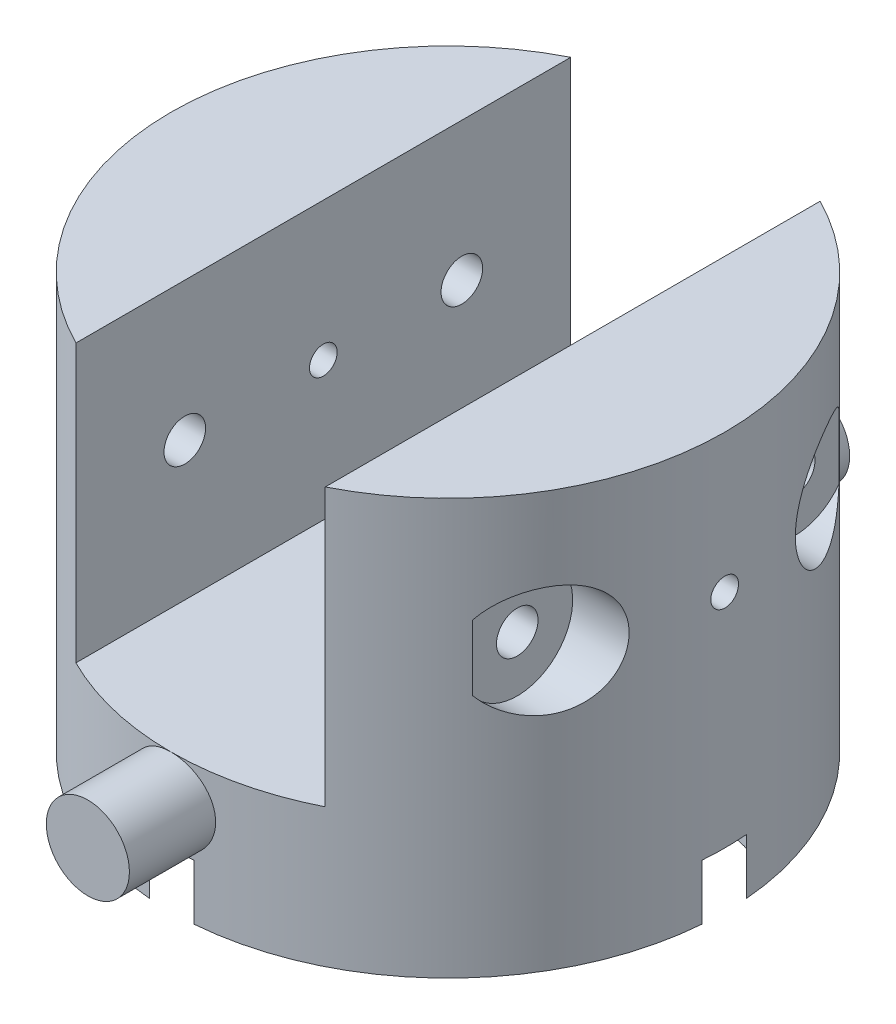
SolidWorks part; units mm, degrees
ref_plane "Front Plane" through (0, 0, 0) normal (0, 0, 1) x (1, 0, 0)
ref_plane "Top Plane" through (0, 0, 0) normal (0, 1, 0) x (1, 0, 0)
ref_plane "Right Plane" through (0, 0, 0) normal (1, 0, 0) x (0, 0, -1)
sketch "Sketch1" plane through (0, 0, 0) normal (0, 1, 0) x (1, 0, 0)
  circle A0 centre (0, 0) radius 10
  circle A1 centre (0, 0) radius 2.5
  dimension "D1" = 20
  dimension "D2" = 5
extrude "Boss-Extrude1" add sketch "Sketch1" along normal blind 5
ref_plane "Plane1" through (0, 0, 10) normal (0, 0, 1) x (1, 0, 0)
sketch "Sketch5" plane through (0, 5, 0) normal (0, 1, 0) x (1, 0, 0)
  line L1 (0, 0) -> (0, 3.5) construction
  line L5 (4.5, 8.9303) -> (4.5, -8.9303)
  line L6 (-4.5, 8.9303) -> (-4.5, -8.9303)
  arc A2 (-4.5, 8.9303) -> (-4.5, -8.9303) centre (0, 0) ccw
  arc A4 (4.5, -8.9303) -> (4.5, 8.9303) centre (0, 0) ccw
  dimension "D1" = 20
  dimension "D2" = 4.5
extrude "Boss-Extrude4" add sketch "Sketch5" along normal blind 10
ref_plane "Plane2" through (-10, 0, 0) normal (-1, 0, 0) x (0, 0, 1)
sketch "Sketch6" plane through (-10, 0, 0) normal (-1, 0, 0) x (0, 0, 1)
  line L0 (8.9303, 15) -> (-8.9303, 15) construction
  line L2 (0, 15) -> (0, 5) construction
  line L3 (10, 5) -> (-10, 5) construction
  line L4 (-8.9303, 5) -> (-10, 5) construction
  circle A0 centre (-5, 10) radius 0.75
  circle A1 centre (5, 10) radius 0.75
  dimension "D1" = 1.5
  dimension "D2" = 5
  dimension "D3" = 5
extrude "Cut-Extrude3" cut sketch "Sketch6" against normal through all contours A0 | A1
sketch "Sketch7" plane through (-10, 0, 0) normal (-1, 0, 0) x (0, 0, 1)
  line L0 (0, 5) -> (0, 15) construction
  line L1 (10, 5) -> (-10, 5) construction
  line L2 (8.9303, 15) -> (-8.9303, 15) construction
  circle A0 centre (-5, 10) radius 2
  circle A1 centre (5, 10) radius 2
  dimension "D1" = 4
extrude "Cut-Extrude4" cut sketch "Sketch7" against normal blind 2.5
ref_plane "Plane3" through (10, 0, 0) normal (1, 0, 0) x (0, 0, -1)
sketch "Sketch8" plane through (10, 0, 0) normal (1, 0, 0) x (0, 0, -1)
  line L0 (0, 5) -> (0, 15) construction
  line L7 (10, 5) -> (-10, 5) construction
  line L8 (8.9303, 15) -> (-8.9303, 15) construction
  circle A0 centre (-5, 10) radius 2
  circle A1 centre (5, 10) radius 2
  dimension "D1" = 4
extrude "Cut-Extrude5" cut sketch "Sketch8" against normal blind 2.5
ref_plane "Plane4" through (0, 0, 10) normal (0, 0, 1) x (1, 0, 0)
sketch "Sketch10" plane through (0, 0, 10) normal (0, 0, 1) x (1, 0, 0)
  line L0 (0, 0) -> (0, 5) construction
  line L1 (4.5, 5) -> (-4.5, 5) construction
  circle A0 centre (0, 3.5) radius 1.5
  dimension "D1" = 3
  dimension "D2" = 1.5
extrude "Boss-Extrude5" add sketch "Sketch10" along normal blind 3 and the other way up to next
mirror "Mirror1" about plane through (0, 0, 0) normal (0, 0, 1) of "Boss-Extrude5"
sketch "Sketch11" plane through (0, 0, 0) normal (1, 0, 0) x (0, 0, -1)
  line L0 (-10, 0) -> (10, 0) construction
  circle A0 centre (0, 10) radius 0.5
  dimension "D1" = 1
  dimension "D2" = 10
extrude "Cut-Extrude6" cut sketch "Sketch11" against normal up to next and the other way up to next
sketch "Sketch12" plane through (0, 0, 0) normal (0, -1, 0) x (1, 0, 0)
  line L0 (-7.6, 0) -> (0, 0) construction
  circle A0 centre (-7.6, 0) radius 2.5
  dimension "D1" = 5
  dimension "D2" = 7.6
extrude "Cut-Extrude7" cut sketch "Sketch12" against normal blind 2
pattern_circular "CirPattern1" count 4 over 360 about axis through (0, 0, 0) along (0, 1, 0) of "Cut-Extrude7"
sketch "Sketch13" plane through (0, 0, 0) normal (0, -1, 0) x (1, 0, 0)
  circle A0 centre (0, 0) radius 4.15
  circle A1 centre (0, 0) radius 5.4
  dimension "D1" = 8.3
  dimension "D2" = 10.8
extrude "Cut-Extrude8" cut sketch "Sketch13" against normal blind 2
